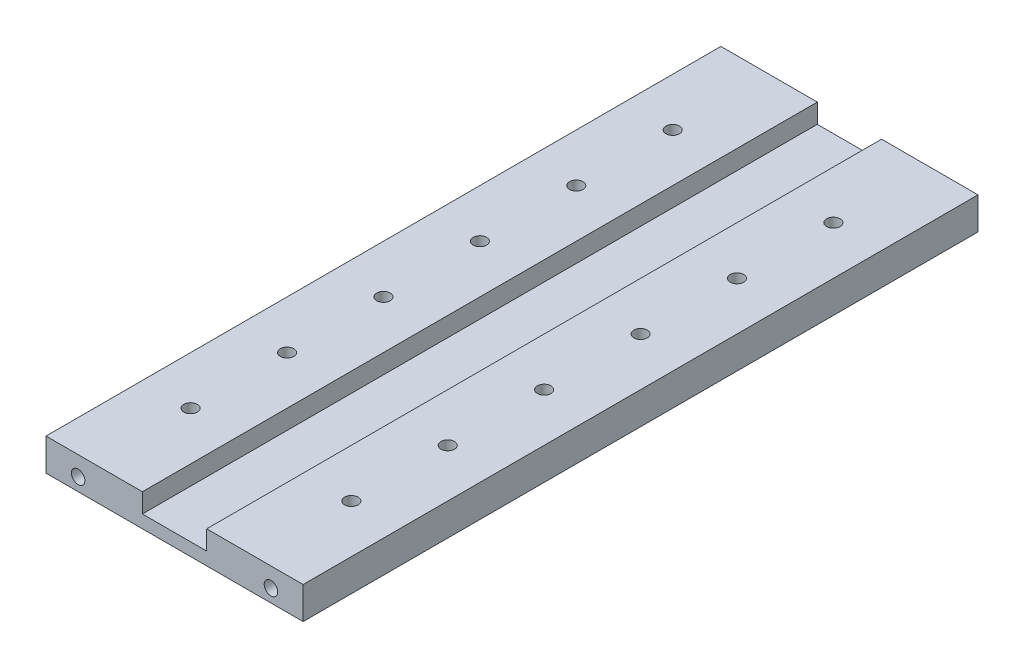
SolidWorks part; units mm, degrees
material "ABS PC"
ref_plane "Ebene vorne" through (0, 0, 0) normal (0, 0, 1) x (1, 0, 0)
ref_plane "Ebene oben" through (0, 0, 0) normal (0, 1, 0) x (1, 0, 0)
ref_plane "Ebene rechts" through (0, 0, 0) normal (1, 0, 0) x (0, 0, -1)
sketch "Skizze1" plane through (0, 0, 0) normal (0, 0, 1) x (1, 0, 0)
  line L0 (-40, 0) -> (40, 0)
  line L1 (40, 0) -> (40, 10)
  line L2 (40, 10) -> (10, 10)
  line L3 (10, 10) -> (10, 4)
  line L4 (10, 4) -> (-10, 4)
  line L5 (-10, 4) -> (-10, 10)
  line L6 (-10, 10) -> (-40, 10)
  line L7 (-40, 10) -> (-40, 0)
  point P3 (0, 0)
  point P10 (0, 4)
  dimension "D1" = 10
  dimension "D2" = 80
  dimension "D3" = 20
  dimension "D4" = 4
extrude "Aufsatz-Linear austragen1" add sketch "Skizze1" along normal mid plane 210
sketch "Skizze3" plane through (0, 0, 0) normal (0, 0, 1) x (1, 0, 0)
  line L0 (-40, 0) -> (40, 0) construction
  line L1 (0, 0) -> (0, 4) construction
  line L2 (10, 4) -> (-10, 4) construction
  point P0 (-25, 4)
  point P1 (25, 4)
  dimension "D1" = 50
  dimension "D2" = 4
hole_wizard "M5 Gewindebohrung1" positions "Skizze5" profile "Skizze6" tap size "M5" standard "DIN"
sketch "Skizze5" plane through (0, 0, 105) normal (0, 0, 1) x (1, 0, 0)
  line L0 (0, 0) -> (0, 10.161) construction
  line L1 (-40, 0) -> (40, 0) construction
  point P0 (-30, 4)
  point P3 (30, 4)
  dimension "D1" = 4
  dimension "D2" = 60
sketch "Skizze6" plane through (-30, 4, 105) normal (1, 0, 0) x (0, -1, 0)
  line L0 (0, 0) -> (0, 15.2618)
  line L1 (0, 15.2618) -> (2.1, 14)
  line L2 (2.1, 14) -> (2.1, 0)
  line L5 (2.1, 0) -> (0, 0)
  line L10 (0, 15.2618) -> (-2.1, 14) construction
  line L11 (0, -6.35) -> (0, 107.95) construction
  dimension "Bohrerdurchmesser" = 4.2
  dimension "Bohrungstiefe" = 14
  dimension "Spitzenwinkel" = 118
cosmetic thread "Bohrungsgewinde1"
cosmetic thread "Bohrungsgewinde2"
hole_wizard "M5 Gewindebohrung2" positions "Skizze8" profile "Skizze9" tap size "M5" standard "DIN"
sketch "Skizze8" plane through (0, 0, -105) normal (0, 0, -1) x (-1, 0, 0)
  line L0 (0, 0) -> (0, 10) construction
  line L1 (40, 0) -> (-40, 0) construction
  line L3 (-40, 10) -> (-10, 10) construction
  point P0 (-25, 5)
  point P3 (25, 5)
  point P18 (0, 5)
  dimension "D1" = 50
sketch "Skizze9" plane through (25, 5, -105) normal (1, 0, 0) x (0, 1, 0)
  line L0 (0, 0) -> (0, 15.2618)
  line L1 (0, 15.2618) -> (2.1, 14)
  line L2 (2.1, 14) -> (2.1, 0)
  line L5 (2.1, 0) -> (0, 0)
  line L10 (0, 15.2618) -> (-2.1, 14) construction
  line L11 (0, -6.35) -> (0, 107.95) construction
  dimension "Bohrerdurchmesser" = 4.2
  dimension "Bohrungstiefe" = 14
  dimension "Spitzenwinkel" = 118
cosmetic thread "Bohrungsgewinde3"
cosmetic thread "Bohrungsgewinde4"
hole_wizard "M5 Gewindebohrung3" positions "Skizze10" profile "Skizze11" tap size "M5" standard "DIN" end condition through all
sketch "Skizze10" plane through (0, 10, 0) normal (0, 1, 0) x (1, 0, 0)
  line L0 (-25, -105) -> (-25, 105) construction
  line L1 (-10, -105) -> (-40, -105) construction
  line L2 (-10, 105) -> (-40, 105) construction
  line L4 (-40, 0) -> (40, 0) construction
  line L5 (-40, -105) -> (-40, 105) construction
  line L6 (40, -105) -> (40, 105) construction
  line L7 (0, -105) -> (0, 105) construction
  line L8 (10, -105) -> (-10, -105) construction
  line L9 (10, 105) -> (-10, 105) construction
  point P17 (-25, -75)
  point P19 (-25, -45)
  point P21 (-25, -15)
  point P24 (-25, 15)
  point P25 (-25, 45)
  point P26 (-25, 75)
  point P36 (25, 75)
  point P37 (25, 45)
  point P38 (25, 15)
  point P39 (25, -15)
  point P40 (25, -45)
  point P41 (25, -75)
  dimension "D1" = 30
  dimension "D2" = 30
  dimension "D3" = 30
sketch "Skizze11" plane through (25, 10, 75) normal (1, 0, 0) x (0, 0, 1)
  line L0 (0, 0) -> (0, 10)
  line L1 (0, 10) -> (2.1, 10)
  line L2 (2.1, 10) -> (2.1, 0)
  line L5 (2.1, 0) -> (0, 0)
  line L11 (0, -6.35) -> (0, 107.95) construction
  dimension "Bohrerdurchmesser" = 4.2
  dimension "Bohrungstiefe" = 10
cosmetic thread "Bohrungsgewinde5"
cosmetic thread "Bohrungsgewinde6"
cosmetic thread "Bohrungsgewinde7"
cosmetic thread "Bohrungsgewinde8"
cosmetic thread "Bohrungsgewinde9"
cosmetic thread "Bohrungsgewinde10"
cosmetic thread "Bohrungsgewinde11"
cosmetic thread "Bohrungsgewinde12"
cosmetic thread "Bohrungsgewinde13"
cosmetic thread "Bohrungsgewinde14"
cosmetic thread "Bohrungsgewinde15"
cosmetic thread "Bohrungsgewinde16"
